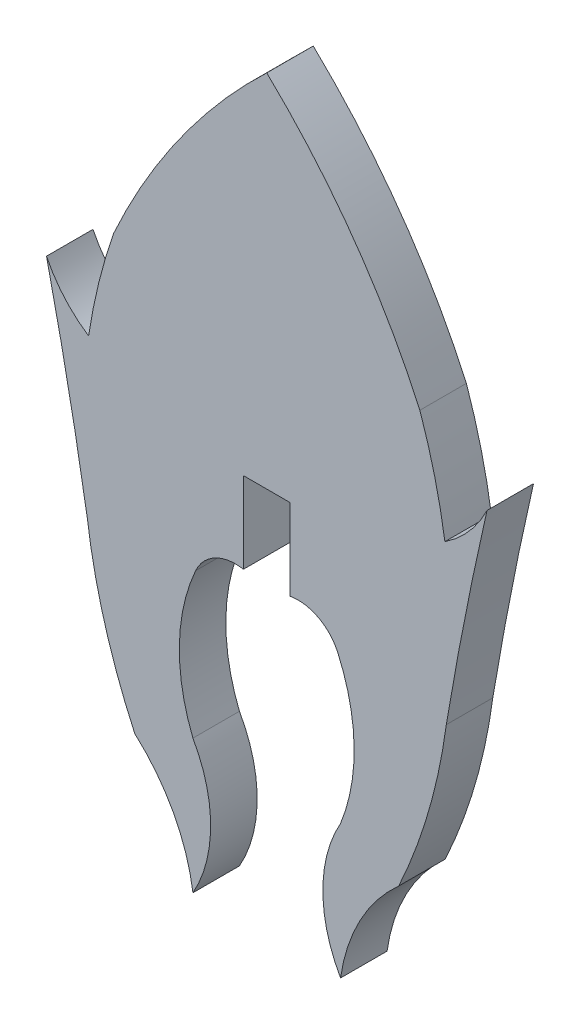
SolidWorks part; units mm, degrees
ref_plane "Front Plane" through (0, 0, 0) normal (0, 0, 1) x (1, 0, 0)
ref_plane "Top Plane" through (0, 0, 0) normal (0, 1, 0) x (1, 0, 0)
ref_plane "Right Plane" through (0, 0, 0) normal (1, 0, 0) x (0, 0, -1)
sketch "Sketch1" plane through (0, 0, 0) normal (0, 0, 1) x (1, 0, 0)
  line L0 (0.7626, -1.9522) -> (0.7628, 0.7071)
  line L1 (0.7628, 0.7071) -> (-0.7612, 0.7071)
  line L2 (-0.7612, 0.7071) -> (-0.7634, -1.9525)
  arc A0 (-5.0171, 5.4541) -> (0.0008, 12.5192) centre (15.5938, -3.8702) cw
  arc A1 (-7.2163, 3.7084) -> (-5.8365, 2.1342) centre (-3.6651, 5.4292) ccw
  arc A2 (2.4199, -7.5707) -> (2.4196, -11.9589) centre (6.2741, -9.7651) ccw
  arc A3 (-5.8822, -3.0382) -> (-7.2163, 3.7084) centre (-120.9925, -22.2938) ccw
  arc A4 (2.4196, -11.9589) -> (4.3243, -8.3965) centre (8.2418, -12.7815) cw
  arc A5 (4.3243, -8.3965) -> (5.8839, -3.0382) centre (-12.4305, -0.6137) ccw
  arc A6 (5.8381, 2.1342) -> (5.0187, 5.4541) centre (-12.4305, -0.6137) ccw
  arc A7 (2.4199, -7.5707) -> (2.3303, -2.7723) centre (-3.2647, -5.2768) ccw
  arc A8 (2.3303, -2.7723) -> (0.7626, -1.9522) centre (1.0275, -3.3544) ccw
  arc A9 (5.8839, -3.0382) -> (7.2179, 3.7084) centre (120.9942, -22.2938) cw
  arc A10 (7.2179, 3.7084) -> (5.8381, 2.1342) centre (3.6667, 5.4292) cw
  arc A11 (5.0187, 5.4541) -> (0.0008, 12.5192) centre (-15.5922, -3.8702) ccw
  arc A12 (-2.3287, -2.7723) -> (-0.761, -1.9522) centre (-1.0258, -3.3544) cw
  arc A13 (-2.4182, -7.5707) -> (-2.3287, -2.7723) centre (3.2664, -5.2768) cw
  arc A14 (-5.8365, 2.1342) -> (-5.0171, 5.4541) centre (12.4321, -0.6137) cw
  arc A15 (-4.3227, -8.3965) -> (-5.8822, -3.0382) centre (12.4321, -0.6137) cw
  arc A16 (-2.4179, -11.9589) -> (-4.3227, -8.3965) centre (-8.2402, -12.7815) ccw
  arc A17 (-2.4182, -7.5707) -> (-2.4179, -11.9589) centre (-6.2725, -9.7651) cw
extrude "Boss-Extrude1" add sketch "Sketch1" along normal blind 1.524 contours A17 A13 A12 L2 L1 L0 A8 A7 A2 A4 A5 A9 A10 A6 A11 A0 A14 A1 A3 A15 A16
